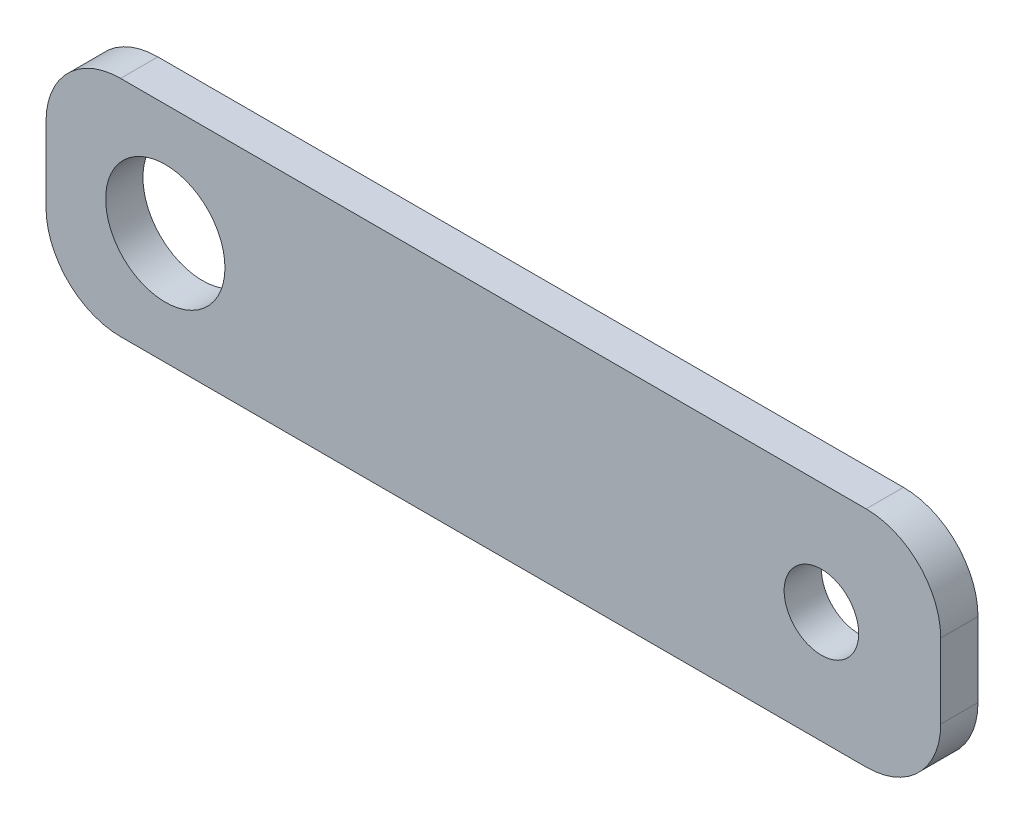
SolidWorks part; units mm, degrees
material "Acier non allié"
ref_plane "Plan de face" through (0, 0, 0) normal (0, 0, 1) x (1, 0, 0)
ref_plane "Plan de dessus" through (0, 0, 0) normal (0, 1, 0) x (1, 0, 0)
ref_plane "Plan de droite" through (0, 0, 0) normal (1, 0, 0) x (0, 0, -1)
sketch "Esquisse1" plane through (0, 0, 0) normal (0, 0, 1) x (1, 0, 0)
  line L1 (60, -15) -> (-60, -15)
  line L2 (60, -15) -> (60, 15)
  line L3 (60, 15) -> (-60, 15)
  line L4 (-60, -15) -> (-60, 15)
  line L5 (60, -15) -> (-60, 15) construction
  line L6 (60, 15) -> (-60, -15) construction
  point P0 (0, 0)
  dimension "D1" = 120
  dimension "D2" = 30
extrude "Boss.-Extru.1" add sketch "Esquisse1" along normal blind 5
sketch "Esquisse2" plane through (0, 0, 5) normal (0, 0, 1) x (1, 0, 0)
  line L0 (-60, 15) -> (-60, -15) construction
  line L1 (60, -15) -> (60, 15) construction
  circle A0 centre (-44, 0) radius 8
  circle A1 centre (44, 0) radius 5
  dimension "D1" = 16
  dimension "D2" = 16
  dimension "D4" = 10
  dimension "D3" = 16
extrude "Enlèv. mat.-Extru.1" cut sketch "Esquisse2" against normal blind 10
fillet "Congé1" radius 10 4 edges at (60, -15, 2.5) (60, 15, 2.5) (-60, -15, 2.5) (-60, 15, 2.5)
